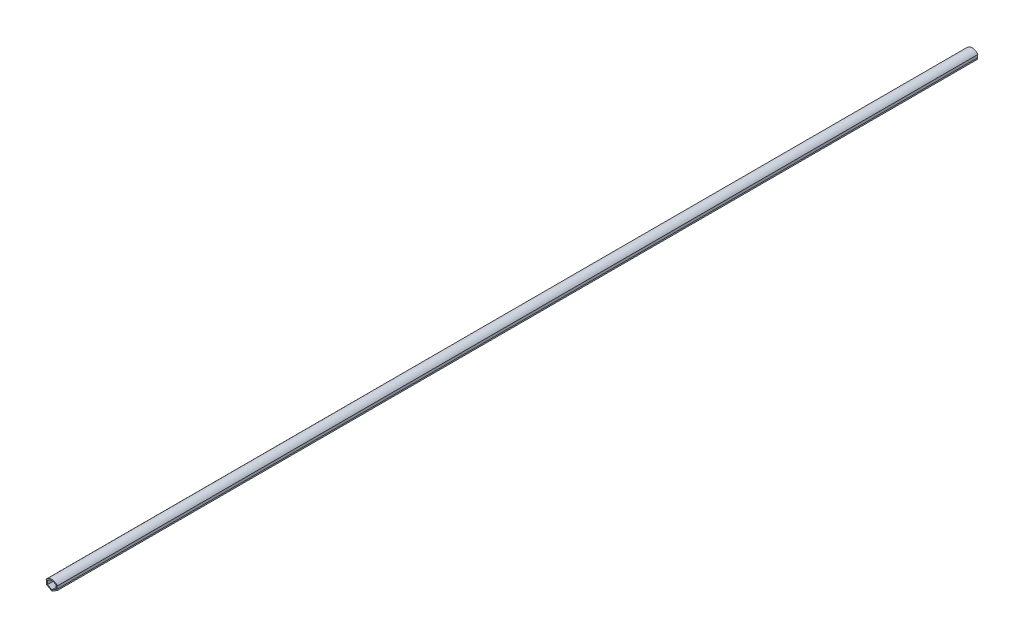
SolidWorks part; units mm, degrees
material "Пластик"
ref_plane "Спереди" through (0, 0, 0) normal (0, 0, 1) x (1, 0, 0)
ref_plane "Сверху" through (0, 0, 0) normal (0, 1, 0) x (1, 0, 0)
ref_plane "Справа" through (0, 0, 0) normal (1, 0, 0) x (0, 0, -1)
sketch "Эскиз1" plane through (0, 0, 0) normal (0, 0, 1) x (1, 0, 0)
  line L42 (0, 0) -> (-6.1, 3.5218)
  line L43 (-6.1, 3.5218) -> (-5.6, 4.3879)
  line L44 (-5.6, 4.3879) -> (-5.6, 8.008)
  line L45 (-5.6, 8.008) -> (-6.2386, 8.008)
  line L46 (0, 0) -> (0, 11) construction
  line L47 (5.6, 8.008) -> (6.2386, 8.008)
  line L48 (5.6, 4.3879) -> (5.6, 8.008)
  line L49 (6.1, 3.5218) -> (5.6, 4.3879)
  line L50 (0, 0) -> (6.1, 3.5218)
  line L51 (0, 1.1547) -> (-4.6, 3.8105)
  line L52 (-4.6, 3.8105) -> (-4.6, 8.008)
  line L53 (4.6, 3.8105) -> (4.6, 8.008)
  line L54 (0, 0) -> (6.1, 3.5218)
  line L55 (0, 1.1547) -> (4.6, 3.8105)
  arc A2 (-6.2386, 8.008) -> (6.2386, 8.008) centre (0, 3) cw
  arc A3 (-4.6, 8.008) -> (4.6, 8.008) centre (0, 3) cw
  dimension "D5" = 8
  dimension "D6" = 6.8
  dimension "D1" = 11.2
  dimension "D2" = 11
  dimension "D3" = 1
  dimension "D4" = 1
  dimension "D7" = 60
  dimension "D8" = 1
extrude "Бобышка-Вытянуть1" add sketch "Эскиз1" along normal blind 1000 contours L42 L46 L51 L52 A3 A2 L45 L44 L43 | L46 L50 L49 L48 L47 A2 A3 L53 L55
